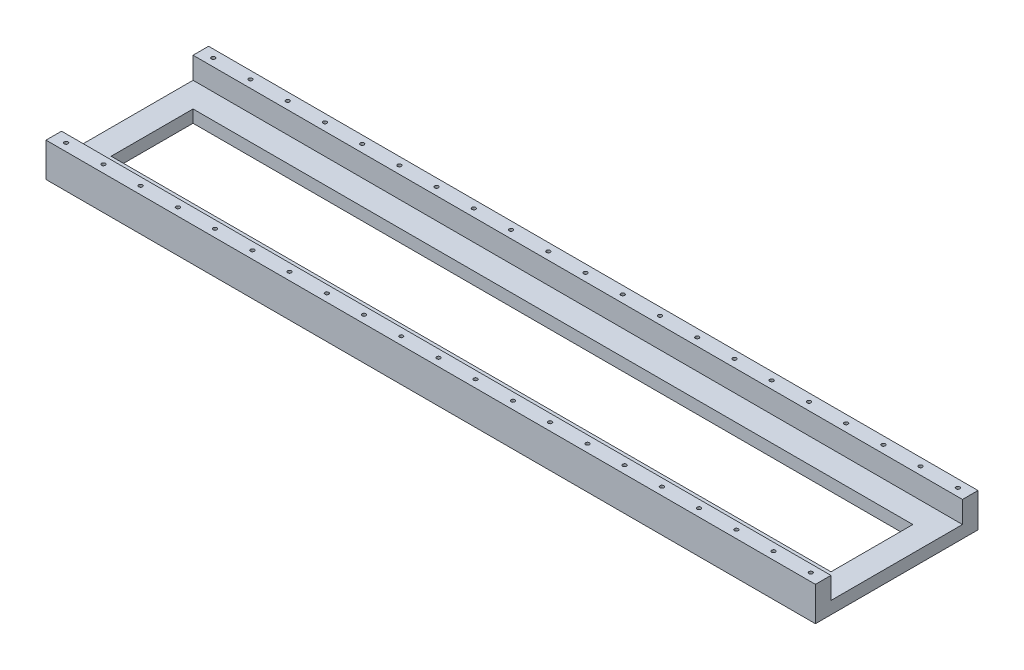
SolidWorks part; units mm, degrees
ref_plane "Front Plane" through (0, 0, 0) normal (0, 0, 1) x (1, 0, 0)
ref_plane "Top Plane" through (0, 0, 0) normal (0, 1, 0) x (1, 0, 0)
ref_plane "Right Plane" through (0, 0, 0) normal (1, 0, 0) x (0, 0, -1)
sketch "Sketch1" plane through (0, 0, 0) normal (0, 1, 0) x (1, 0, 0)
  line L1 (0, 0) -> (1240, 0)
  line L2 (0, 0) -> (0, 262)
  line L3 (0, 262) -> (1240, 262)
  line L4 (1240, 0) -> (1240, 262)
extrude "Boss-Extrude1" add sketch "Sketch1" along normal blind 20 contours L2 L3 L4 L1
sketch "Sketch2" plane through (0, 20, 0) normal (0, 1, 0) x (1, 0, 0)
  line L0 (1240, 0) -> (1240, 262) construction
  line L1 (0, 0) -> (1240, 0)
  line L2 (0, 0) -> (0, 25)
  line L3 (0, 25) -> (1240, 25)
  line L4 (1240, 0) -> (1240, 25)
  line L5 (0, 0) -> (1240, 0) construction
  line L6 (0, 0) -> (0, 262) construction
  line L7 (0, 262) -> (1240, 262)
  line L8 (0, 262) -> (0, 237)
  line L9 (0, 237) -> (1240, 237)
  line L10 (1240, 262) -> (1240, 237)
extrude "Boss-Extrude2" add sketch "Sketch2" along normal blind 35
sketch "Sketch3" plane through (0, 55, 0) normal (0, 1, 0) x (1, 0, 0)
  circle A0 centre (20, 12.5) radius 3
  circle A1 centre (80, 12.5) radius 3
  circle A2 centre (140, 12.5) radius 3
  circle A3 centre (200, 12.5) radius 3
  circle A4 centre (260, 12.5) radius 3
  circle A5 centre (320, 12.5) radius 3
  circle A6 centre (380, 12.5) radius 3
  circle A7 centre (440, 12.5) radius 3
  circle A8 centre (500, 12.5) radius 3
  circle A9 centre (560, 12.5) radius 3
  circle A10 centre (620, 12.5) radius 3
  circle A11 centre (680, 12.5) radius 3
  circle A12 centre (740, 12.5) radius 3
  circle A13 centre (800, 12.5) radius 3
  circle A14 centre (860, 12.5) radius 3
  circle A15 centre (920, 12.5) radius 3
  circle A16 centre (980, 12.5) radius 3
  circle A17 centre (1040, 12.5) radius 3
  circle A18 centre (1100, 12.5) radius 3
  circle A19 centre (1160, 12.5) radius 3
  circle A20 centre (1220, 12.5) radius 3
  dimension "D1" = 21
sketch "Sketch4" plane through (0, 55, 0) normal (0, 1, 0) x (1, 0, 0)
  circle A0 centre (20, 249.5) radius 3
  circle A1 centre (80, 249.5) radius 3
  circle A2 centre (140, 249.5) radius 3
  circle A3 centre (200, 249.5) radius 3
  circle A4 centre (260, 249.5) radius 3
  circle A5 centre (320, 249.5) radius 3
  circle A6 centre (380, 249.5) radius 3
  circle A7 centre (440, 249.5) radius 3
  circle A8 centre (500, 249.5) radius 3
  circle A9 centre (560, 249.5) radius 3
  circle A10 centre (620, 249.5) radius 3
  circle A11 centre (680, 249.5) radius 3
  circle A12 centre (740, 249.5) radius 3
  circle A13 centre (800, 249.5) radius 3
  circle A14 centre (860, 249.5) radius 3
  circle A15 centre (920, 249.5) radius 3
  circle A16 centre (980, 249.5) radius 3
  circle A17 centre (1040, 249.5) radius 3
  circle A18 centre (1100, 249.5) radius 3
  circle A19 centre (1160, 249.5) radius 3
  circle A20 centre (1220, 249.5) radius 3
  dimension "D1" = 21
extrude "Cut-Extrude1" cut sketch "Sketch3" against normal blind 10
extrude "Cut-Extrude2" cut sketch "Sketch4" against normal blind 10
sketch "Sketch5" plane through (0, 20, 0) normal (0, 1, 0) x (1, 0, 0)
  line L1 (40, 65) -> (1200, 65)
  line L2 (40, 65) -> (40, 197)
  line L3 (40, 197) -> (1200, 197)
  line L4 (1200, 65) -> (1200, 197)
  point P4 (0, 0)
  point P5 (0, 0)
extrude "Cut-Extrude3" cut sketch "Sketch5" against normal through all
